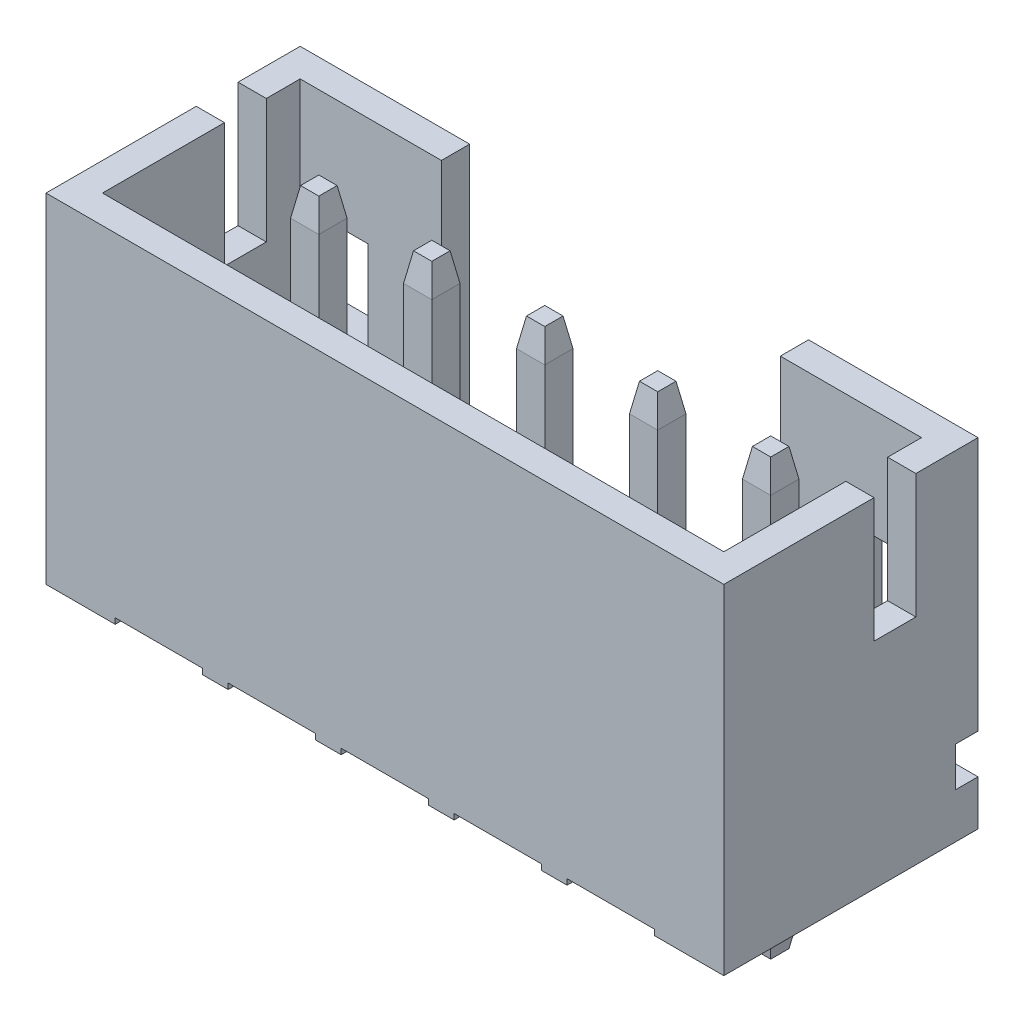
SolidWorks part; units mm, degrees
ref_plane "Front Plane" through (0, 0, 0) normal (0, 0, 1) x (1, 0, 0)
ref_plane "Top Plane" through (0, 0, 0) normal (0, 1, 0) x (1, 0, 0)
ref_plane "Right Plane" through (0, 0, 0) normal (1, 0, 0) x (0, 0, -1)
sketch "Sketch1" plane through (0, 0, 0) normal (0, 1, 0) x (1, 0, 0)
  line L1 (-6, 2.25) -> (6, 2.25)
  line L2 (-6, 2.25) -> (-6, -2.25)
  line L3 (-6, -2.25) -> (6, -2.25)
  line L4 (6, 2.25) -> (6, -2.25)
  dimension "D1" = 12
  dimension "D2" = 4.5
  dimension "D3" = 2.25
  dimension "D4" = 6
extrude "Extrude1" add sketch "Sketch1" along normal blind 6
sketch "Sketch2" plane through (0, 0, 2.25) normal (0, 0, 1) x (1, 0, 0)
  line L0 (-6, 0) -> (6, 0) construction
  line L6 (-0.775, 0.1) -> (0.775, 0.1)
  line L7 (-0.775, 0.1) -> (-0.775, 0)
  line L8 (-0.775, 0) -> (0, 0)
  line L9 (0.775, 0.1) -> (0.775, 0)
  line L10 (0, 0) -> (0.775, 0)
  dimension "D1" = 0.1
  dimension "D3" = 1.55
extrude "Cut-Extrude1" cut sketch "Sketch2" against normal through all
sketch "Sketch3" plane through (0, 6, 0) normal (0, 1, 0) x (-1, 0, 0)
  line L0 (-6, -2.25) -> (6, -2.25) construction
  line L1 (5.5, -1.75) -> (-5.5, -1.75)
  line L2 (5.5, -1.75) -> (5.5, 1.75)
  line L3 (5.5, 1.75) -> (-5.5, 1.75)
  line L4 (-5.5, -1.75) -> (-5.5, 1.75)
  line L5 (6, 2.25) -> (-6, 2.25) construction
  line L6 (-6, 2.25) -> (-6, -2.25) construction
  line L7 (6, -2.25) -> (6, 2.25) construction
  dimension "D1" = 0.5
  dimension "D2" = 0.5
  dimension "D3" = 0.5
  dimension "D4" = 0.5
extrude "Cut-Extrude2" cut sketch "Sketch3" against normal offset from surface (4.2 mm away) 1.8 up to face at (3.3875, 0, 0)
sketch "Sketch5" plane through (-6, 0, 0) normal (-1, 0, 0) x (0, 0, 1)
  line L1 (-1.15, 6) -> (-0.41, 6)
  line L2 (-1.15, 6) -> (-1.15, 3.8)
  line L3 (-1.15, 3.8) -> (-0.41, 3.8)
  line L4 (-0.41, 6) -> (-0.41, 3.8)
  line L5 (-2.25, 6) -> (-2.25, 0) construction
  line L6 (-2.25, 6) -> (2.25, 6) construction
  dimension "D1" = 2.2
  dimension "D2" = 0.74
  dimension "D3" = 1.1
extrude "Cut-Extrude3" cut sketch "Sketch5" against normal through all
sketch "Sketch6" plane through (0, 0, -2.25) normal (0, 0, -1) x (-1, 0, 0)
  line L1 (-6, 6) -> (6, 6) construction
  line L2 (-3, 6) -> (3, 6)
  line L3 (-3, 6) -> (-3, 2)
  line L4 (-3, 2) -> (3, 2)
  line L5 (3, 6) -> (3, 2)
  dimension "D1" = 6
  dimension "D2" = 3
  dimension "D3" = 4
extrude "Cut-Extrude4" cut sketch "Sketch6" against normal blind 1.2
ref_plane "Plane1" through (0, 8.5, 0) normal (0, 1, 0) x (-1, 0, 0)
sketch "Sketch8" plane through (0, 8.5, 0) normal (0, 1, 0) x (-1, 0, 0)
  line L0 (-6, 2.25) -> (-6, -2.25) construction
  line L1 (6, -2.25) -> (6, 2.25) construction
  line L2 (-6, 2.25) -> (-6, -2.25)
  line L3 (6, -2.25) -> (6, 2.25)
  line L4 (-6, 2.25) -> (6, 2.25)
  line L5 (6, -2.25) -> (-6, -2.25)
sketch "Sketch9" plane through (0, 0, 0) normal (1, 0, 0) x (0, 0, -1)
  line L0 (2.25, 6) -> (2.25, 0) construction
  line L1 (2.25, 1.5) -> (1.85, 1.5)
  line L2 (2.25, 1.5) -> (2.25, 0.8)
  line L3 (2.25, 0.8) -> (1.85, 0.8)
  line L4 (1.85, 1.5) -> (1.85, 0.8)
  line L5 (2.25, 0) -> (-2.25, 0) construction
  line L6 (-2.25, 6) -> (-2.25, 0) construction
  dimension "D1" = 0.8
  dimension "D2" = 0.7
  dimension "D3" = 4.1
extrude "Cut-Extrude5" cut sketch "Sketch9" against normal through all and the other way through all
sketch "Sketch10" plane through (0, 0, -2.25) normal (0, 0, -1) x (-1, 0, 0)
  line L0 (-5.5, 1.8) -> (-5.5, 6) construction
  line L1 (-5.5, 4.0716) -> (-4.3, 4.0716)
  line L2 (-5.5, 4.0716) -> (-5.5, 2.4716)
  line L3 (-5.5, 2.4716) -> (-4.3, 2.4716)
  line L4 (-4.3, 4.0716) -> (-4.3, 2.4716)
  line L5 (5.5, 1.8) -> (5.5, 6) construction
  line L6 (5.5, 4.0716) -> (4.3, 4.0716)
  line L7 (5.5, 4.0716) -> (5.5, 2.4716)
  line L8 (5.5, 2.4716) -> (4.3, 2.4716)
  line L9 (4.3, 4.0716) -> (4.3, 2.4716)
  dimension "D1" = 1.2
  dimension "D2" = 1.6
extrude "Cut-Extrude6" cut sketch "Sketch10" against normal up to surface (0.5 mm away) up to face at (0, 3.95, -1.75)
sketch "Sketch11" plane through (0, 0, 0) normal (1, 0, 0) x (0, 0, -1)
  line L0 (0, 1.8) -> (-0.5764, 1.2236)
  line L1 (-1.75, 1.8) -> (1.75, 1.8) construction
  line L2 (-0.5764, 1.2236) -> (-1.75, 1.2236)
  line L3 (-1.75, 1.2236) -> (-1.75, 1.8)
  line L4 (-1.75, 1.8) -> (0, 1.8)
extrude "Cut-Extrude7" cut sketch "Sketch11" against normal up to surface and the other way up to surface
pattern_linear "LPattern4" count 3 spacing 2 along (1, 0, 0) count 3 spacing 2 along (-1, 0, 0) of "Cut-Extrude1"
sketch "Sketch7" plane through (0, 0, 0) normal (0, 1, 0) x (1, 0, 0)
  line L0 (0, 0.33) -> (0.25, 0.33)
  line L1 (-0.25, 0.33) -> (0, 0.33)
  line L2 (-0.25, 0.33) -> (-0.25, 0.83)
  line L3 (-0.25, 0.83) -> (0.25, 0.83)
  line L4 (0.25, 0.33) -> (0.25, 0.83)
  line L5 (0.775, 2.25) -> (-0.775, 2.25) construction
  dimension "D1" = 0.5
  dimension "D2" = 0.5
  dimension "D3" = 1.42
extrude "Extrude2" add sketch "Sketch7" along normal offset from surface 0.3 and the other way blind 2 up to face at (0, 6, 0.795)
pattern_linear "LPattern2" count 3 spacing 2 along (1, 0, 0) count 3 spacing 2 along (-1, 0, 0) of "Extrude2"
chamfer "Chamfer1" distance 0.5 angle 10 40 edges at (0, -2, -0.33) (0.25, -2, -0.58) (0, -2, -0.83) (-0.25, -2, -0.58) (0.25, 5.7, -0.58) (0, 5.7, -0.33) (-0.25, 5.7, -0.58) (0, 5.7, -0.83) (4.25, 5.7, -0.58) (4, 5.7, -0.83) (4, 5.7, -0.33) (3.75, 5.7, -0.58) (-3.75, 5.7, -0.58) (-4, 5.7, -0.83) (-4, 5.7, -0.33) (-4.25, 5.7, -0.58) (-1.75, 5.7, -0.58) (-2, 5.7, -0.83) (-2, 5.7, -0.33) (-2.25, 5.7, -0.58) (2.25, 5.7, -0.58) (2, 5.7, -0.83) (2, 5.7, -0.33) (1.75, 5.7, -0.58) (4, -2, -0.83) (4, -2, -0.33) (4.25, -2, -0.58) (3.75, -2, -0.58) (2, -2, -0.83) (2, -2, -0.33) (2.25, -2, -0.58) (1.75, -2, -0.58) (-2, -2, -0.83) (-2, -2, -0.33) (-1.75, -2, -0.58) (-2.25, -2, -0.58) (-4, -2, -0.83) (-4, -2, -0.33) (-3.75, -2, -0.58) (-4.25, -2, -0.58)
sketch "Component_Outline" plane through (0, 0, 0) normal (0, 1, 0) x (1, 0, 0)
  line L1 (-6, -2.25) -> (6, -2.25)
  line L2 (-6, -2.25) -> (-6, 2.25)
  line L3 (-6, 2.25) -> (6, 2.25)
  line L4 (6, -2.25) -> (6, 2.25)
